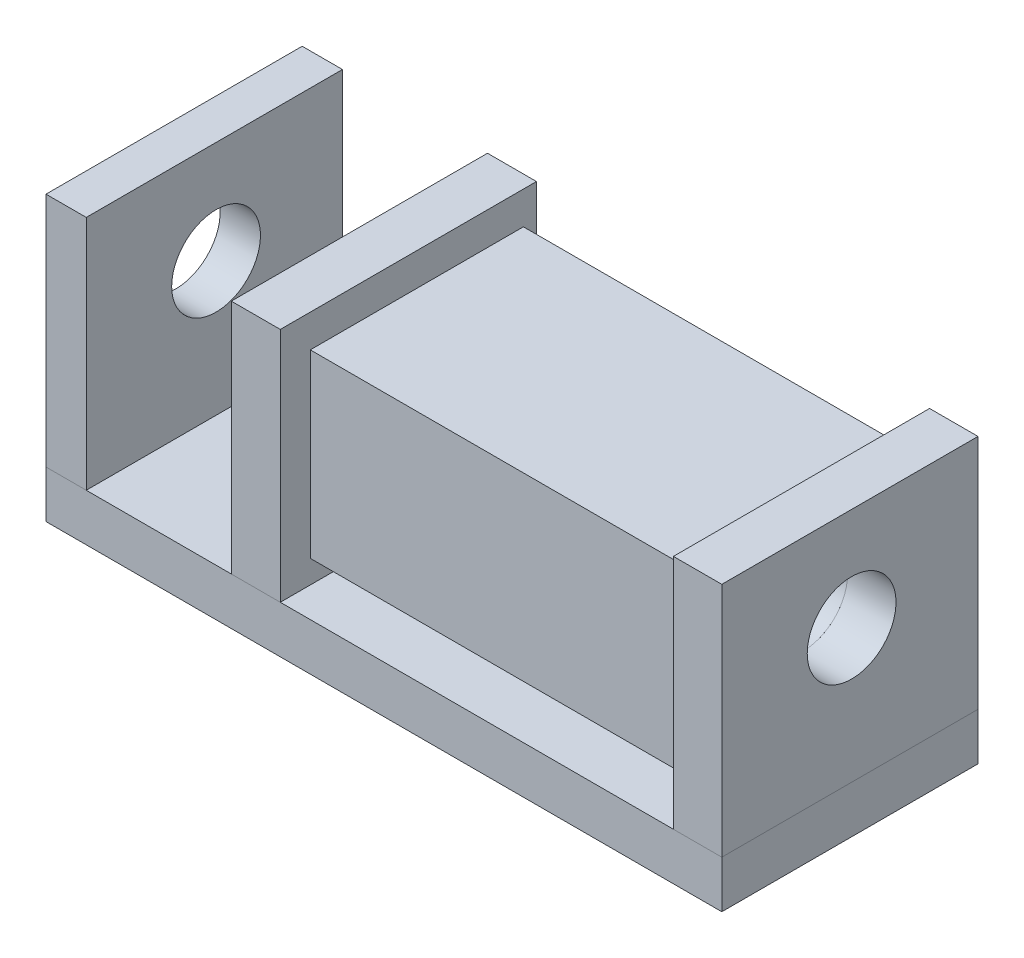
SolidWorks part; units mm, degrees
ref_plane "Ebene vorne" through (0, 0, 0) normal (0, 0, 1) x (1, 0, 0)
ref_plane "Ebene oben" through (0, 0, 0) normal (0, 1, 0) x (1, 0, 0)
ref_plane "Ebene rechts" through (0, 0, 0) normal (1, 0, 0) x (0, 0, -1)
sketch "Skizze1" plane through (0, 0, 0) normal (0, 1, 0) x (1, 0, 0)
  line L1 (0, 0) -> (142.9929, 0)
  line L2 (0, 0) -> (0, 54.2065)
  line L3 (0, 54.2065) -> (142.9929, 54.2065)
  line L4 (142.9929, 0) -> (142.9929, 54.2065)
extrude "Aufsatz-Linear austragen1" add sketch "Skizze1" along normal blind 10
sketch "Skizze2" plane through (0, 10, 0) normal (0, 1, 0) x (1, 0, 0)
  line L0 (142.9929, 54.2065) -> (0, 54.2065) construction
  line L1 (0, 0) -> (8.5187, 0)
  line L2 (0, 0) -> (0, 54.2065)
  line L3 (0, 54.2065) -> (8.5187, 54.2065)
  line L4 (8.5187, 0) -> (8.5187, 54.2065)
  line L6 (142.9929, 0) -> (132.7469, 0)
  line L7 (142.9929, 0) -> (142.9929, 54.2065)
  line L8 (142.9929, 54.2065) -> (132.7469, 54.2065)
  line L9 (132.7469, 0) -> (132.7469, 54.2065)
extrude "Aufsatz-Linear austragen2" add sketch "Skizze2" along normal blind 50 separate body
sketch "Skizze3" plane through (0, 10, 0) normal (0, 1, 0) x (1, 0, 0)
  line L0 (142.9929, 54.2065) -> (0, 54.2065) construction
  line L1 (39.2104, 54.2065) -> (49.5738, 54.2065)
  line L2 (39.2104, 54.2065) -> (39.2104, 0)
  line L3 (39.2104, 0) -> (49.5738, 0)
  line L4 (49.5738, 54.2065) -> (49.5738, 0)
  line L5 (0, 0) -> (142.9929, 0) construction
extrude "Aufsatz-Linear austragen3" add sketch "Skizze3" along normal blind 50 separate body
sketch "Skizze4" plane through (49.5738, 0, 0) normal (1, 0, 0) x (0, 0, -1)
  line L1 (6.3478, 53.082) -> (51.4371, 53.082)
  line L2 (6.3478, 53.082) -> (6.3478, 14.8769)
  line L3 (6.3478, 14.8769) -> (51.4371, 14.8769)
  line L4 (51.4371, 53.082) -> (51.4371, 14.8769)
extrude "Optional" add sketch "Skizze4" along normal up to next (83.1731 mm away) separate body
sketch "Skizze5" plane through (0, 0, 0) normal (-1, 0, 0) x (0, 0, 1)
  circle A0 centre (-27.464, 38.2969) radius 9.3919
extrude "Schnitt-Linear austragen1" cut sketch "Skizze5" against normal up to surface (142.9929 mm away) up to face at (142.9929, 35, -27.1032)
